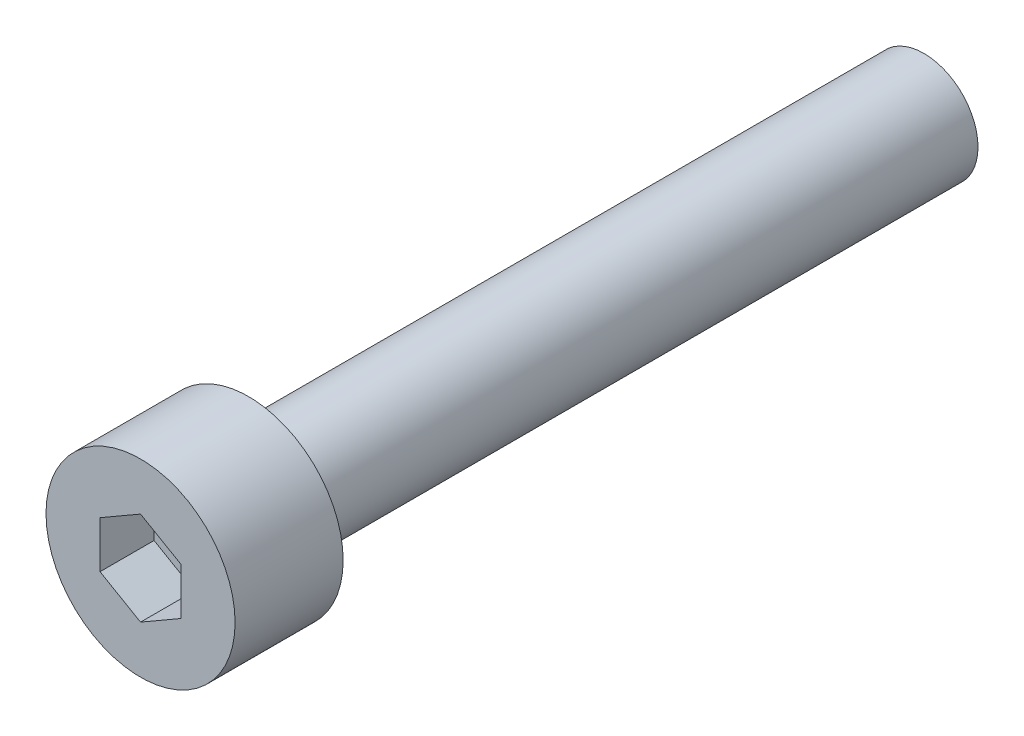
SolidWorks part; units mm, degrees
ref_plane "Front Plane" through (0, 0, 0) normal (0, 0, 1) x (1, 0, 0)
ref_plane "Top Plane" through (0, 0, 0) normal (0, 1, 0) x (1, 0, 0)
ref_plane "Right Plane" through (0, 0, 0) normal (1, 0, 0) x (0, 0, -1)
sketch "Sketch1" plane through (0, 0, 0) normal (0, 0, 1) x (1, 0, 0)
  circle A0 centre (0, 0) radius 3.5
extrude "Boss-Extrude1" add sketch "Sketch1" along normal blind 4
sketch "Sketch2" plane through (0, 0, 4) normal (0, 0, 1) x (1, 0, 0)
  line L1 (0, -1.7321) -> (1.5, -0.866)
  line L2 (1.5, -0.866) -> (1.5, 0.866)
  line L3 (1.5, 0.866) -> (0, 1.7321)
  line L4 (0, 1.7321) -> (-1.5, 0.866)
  line L5 (-1.5, 0.866) -> (-1.5, -0.866)
  line L6 (-1.5, -0.866) -> (0, -1.7321)
  circle A0 centre (0, 0) radius 1.5 construction
  dimension "D1" = 3
extrude "Cut-Extrude1" cut sketch "Sketch2" against normal blind 2
sketch "Sketch3" plane through (0, 0, 0) normal (0, 0, -1) x (-1, 0, 0)
  circle A0 centre (0, 0) radius 2
extrude "Boss-Extrude2" add sketch "Sketch3" along normal blind 25
